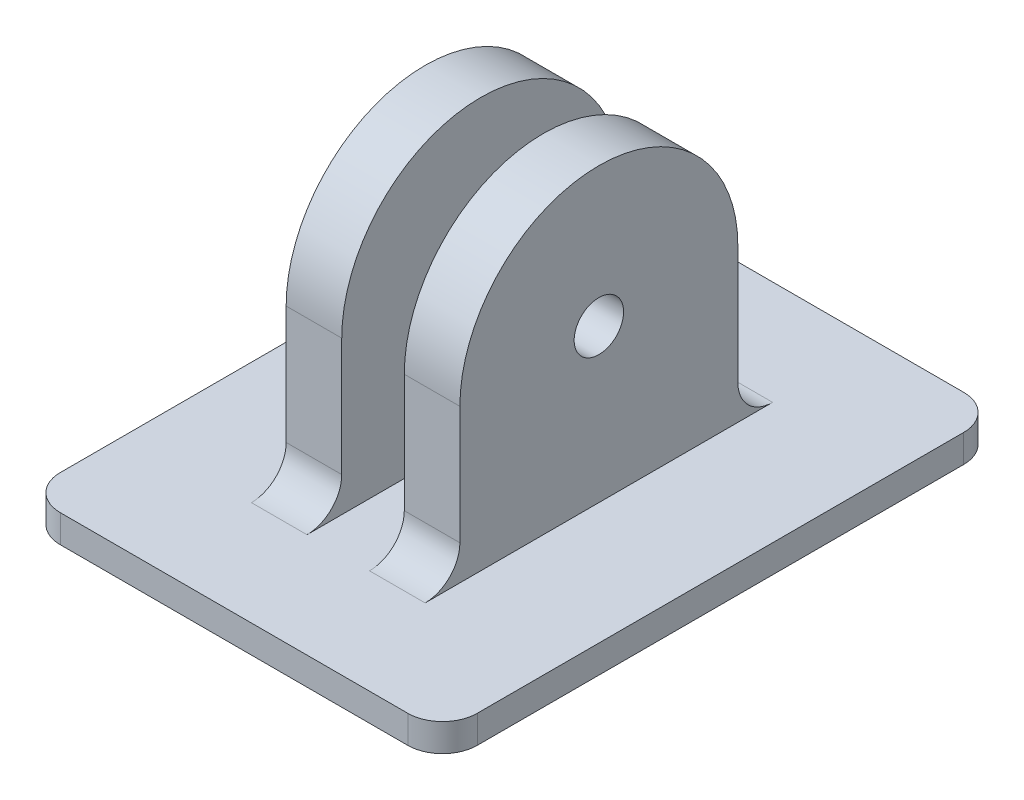
SolidWorks part; units mm, degrees
ref_plane "Plan de face" through (0, 0, 0) normal (0, 0, 1) x (1, 0, 0)
ref_plane "Plan de dessus" through (0, 0, 0) normal (0, 1, 0) x (1, 0, 0)
ref_plane "Plan de droite" through (0, 0, 0) normal (1, 0, 0) x (0, 0, -1)
sketch "Esquisse1" plane through (0, 0, 0) normal (0, 1, 0) x (1, 0, 0)
  line L1 (-15, 20) -> (15, 20)
  line L2 (-15, 20) -> (-15, -20)
  line L3 (-15, -20) -> (15, -20)
  line L4 (15, 20) -> (15, -20)
  point P4 (15, 0)
  point P6 (0, 20)
  dimension "D1" = 30
  dimension "D2" = 40
  dimension "D3" = 0
  dimension "D4" = 0
extrude "Boss.-Extru.1" add sketch "Esquisse1" along normal blind 2
sketch "Esquisse2" plane through (0, 2, 0) normal (0, 1, 0) x (1, 0, 0)
  line L0 (0, 0) -> (0, 10.1467) construction
  line L1 (2.25, 10) -> (6.25, 10)
  line L2 (2.25, 10) -> (2.25, -10)
  line L3 (2.25, -10) -> (6.25, -10)
  line L4 (6.25, 10) -> (6.25, -10)
  line L5 (-2.25, -10) -> (-6.25, -10)
  line L6 (-2.25, 10) -> (-6.25, 10)
  line L7 (-6.25, 10) -> (-6.25, -10)
  line L8 (-2.25, 10) -> (-2.25, -10)
  point P10 (2.25, 0)
  dimension "D1" = 2.25
  dimension "D2" = 20
  dimension "D3" = 4
  dimension "D4" = 0
extrude "Boss.-Extru.2" add sketch "Esquisse2" along normal blind 11
sketch "Esquisse3" plane through (-6.25, 0, 0) normal (-1, 0, 0) x (0, 0, 1)
  line L0 (-10, 13) -> (10, 13)
  arc A0 (-10, 13) -> (10, 13) centre (0, 13) cw
extrude "Boss.-Extru.3" add sketch "Esquisse3" against normal up to vertex
sketch "Esquisse4" plane through (6.25, 0, 0) normal (1, 0, 0) x (0, 0, -1)
  line L1 (10, 13) -> (-10, 13)
  arc A0 (-10, 13) -> (10, 13) centre (0, 13) cw
extrude "Boss.-Extru.4" add sketch "Esquisse4" against normal up to vertex
sketch "Esquisse5" plane through (6.25, 0, 0) normal (1, 0, 0) x (0, 0, -1)
  circle A0 centre (0, 13) radius 1.778
extrude "Enlèv. mat.-Extru.1" cut sketch "Esquisse5" against normal up to surface (12.5 mm away) up to face at (-6.25, 10, 0)
fillet "Congé1" radius 2.5 8 edges at (4.25, 2, -10) (15, 1, -20) (-15, 1, -20) (-4.25, 2, -10) (15, 1, 20) (-15, 1, 20) (4.25, 2, 10) (-4.25, 2, 10)
